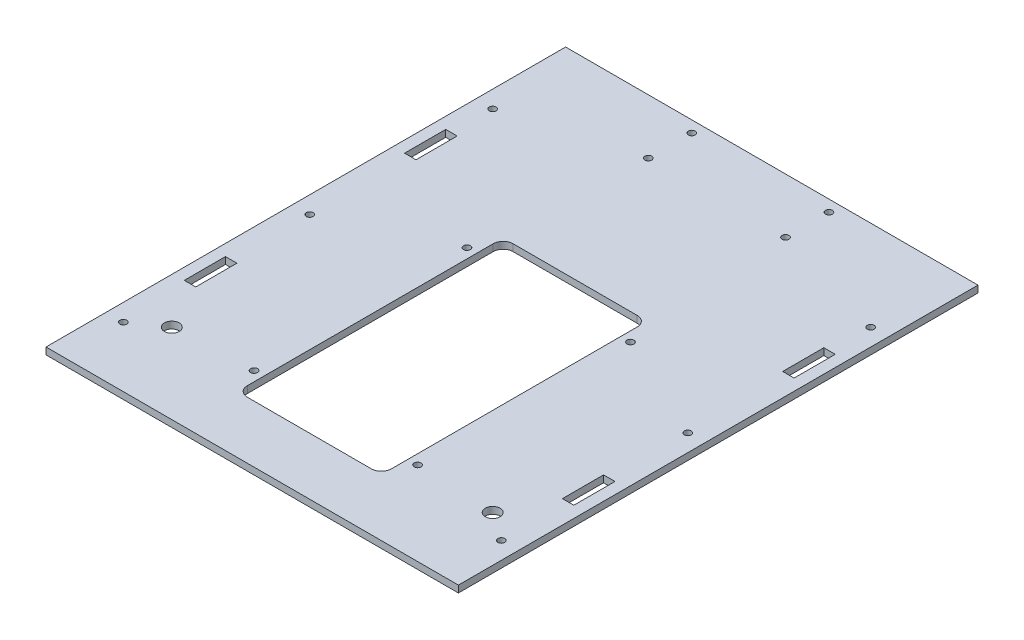
SolidWorks part; units mm, degrees
material "PMMA"
ref_plane "Front Plane" through (0, 0, 0) normal (0, 0, 1) x (1, 0, 0)
ref_plane "Top Plane" through (0, 0, 0) normal (0, 1, 0) x (1, 0, 0)
ref_plane "Right Plane" through (0, 0, 0) normal (1, 0, 0) x (0, 0, -1)
sketch "Schizzo1" plane through (0, 0, 0) normal (0, 1, 0) x (1, 0, 0)
  line L0 (90.17, 113.61) -> (-90.17, -113.61) construction
  line L1 (-90.17, 113.61) -> (90.17, 113.61)
  line L2 (-90.17, 113.61) -> (-90.17, -113.61)
  line L3 (-90.17, -113.61) -> (90.17, -113.61)
  line L4 (90.17, 113.61) -> (90.17, -113.61)
  point P4 (0, 0)
  dimension "D1" = 227.22
  dimension "D2" = 180.34
extrude "Estrusione-Estrusione1" add sketch "Schizzo1" along normal blind 3
sketch "Schizzo3" plane through (0, 0, 0) normal (0, 1, 0) x (1, 0, 0)
  line L0 (0, 113.61) -> (0, -113.61) construction
  line L1 (-31.5, -88.61) -> (-31.5, 27.62) construction
  line L2 (-31.5, -88.61) -> (31.5, -88.61) construction
  line L3 (31.5, -88.61) -> (31.5, 27.62) construction
  line L4 (-31.5, 27.62) -> (31.5, 27.62) construction
  line L5 (90.17, 113.61) -> (-90.17, 113.61) construction
  line L6 (-90.17, -113.61) -> (90.17, -113.61) construction
  line L7 (-31.5, -84.26) -> (-31.5, 23.27)
  line L8 (-27.15, -88.61) -> (27.15, -88.61)
  line L9 (31.5, -84.26) -> (31.5, 23.27)
  line L10 (-27.15, 27.62) -> (27.15, 27.62)
  line L11 (-35.75, -77.045) -> (35.75, -77.045) construction
  line L12 (0, 27.62) -> (0, -88.61) construction
  line L13 (-35.75, 16.055) -> (-35.75, -77.045) construction
  line L14 (-35.75, 16.055) -> (35.75, 16.055) construction
  line L15 (35.75, -77.045) -> (35.75, 16.055) construction
  arc A0 (-31.5, -84.26) -> (-27.15, -88.61) centre (-27.15, -84.26) ccw
  arc A1 (31.5, -84.26) -> (27.15, -88.61) centre (27.15, -84.26) cw
  arc A2 (27.15, 27.62) -> (31.5, 23.27) centre (27.15, 23.27) cw
  arc A3 (-31.5, 23.27) -> (-27.15, 27.62) centre (-27.15, 23.27) cw
  circle A4 centre (-35.75, -77.045) radius 1.5
  circle A5 centre (35.75, -77.045) radius 1.5
  circle A6 centre (-35.75, 16.055) radius 1.5
  circle A7 centre (35.75, 16.055) radius 1.5
  point P29 (0, -77.045)
  dimension "D12" = 3
  dimension "D1" = 116.23
  dimension "D2" = 63
  dimension "D4" = 4.35
  dimension "D5" = 4.35
  dimension "D6" = 4.35
  dimension "D7" = 4.35
  dimension "D8" = 4.35
  dimension "D9" = 4.35
  dimension "D10" = 4.35
  dimension "D11" = 4.35
  dimension "D13" = 71.5
  dimension "D14" = 93.1
  dimension "D3" = 25
  dimension "D15" = 116.23
  dimension "D16" = 11.565
  dimension "D17" = 11.565
sketch "Schizzo2" plane through (0, 0, 0) normal (0, 1, 0) x (1, 0, 0)
  line L0 (90.17, -113.61) -> (90.17, 113.61) construction
  line L1 (85.17, -40.13) -> (80.17, -40.13)
  line L2 (85.17, -40.13) -> (85.17, -58.13)
  line L3 (85.17, -58.13) -> (80.17, -58.13)
  line L4 (80.17, -40.13) -> (80.17, -58.13)
  line L5 (-90.17, -113.61) -> (90.17, -113.61) construction
  line L6 (0, -113.61) -> (0, 113.61) construction
  line L7 (90.17, 113.61) -> (-90.17, 113.61) construction
  line L8 (-85.17, -40.13) -> (-80.17, -40.13)
  line L9 (-85.17, -40.13) -> (-85.17, -58.13)
  line L10 (-85.17, -58.13) -> (-80.17, -58.13)
  line L11 (-80.17, -40.13) -> (-80.17, -58.13)
  line L12 (-82.67, 113.61) -> (-82.67, -113.61) construction
  line L13 (-90.17, -78.61) -> (90.17, -78.61) construction
  line L14 (-85.17, 38.19) -> (-80.17, 38.19)
  line L15 (-85.17, 38.19) -> (-85.17, 56.19)
  line L16 (-85.17, 56.19) -> (-80.17, 56.19)
  line L17 (-80.17, 38.19) -> (-80.17, 56.19)
  line L18 (85.17, 38.19) -> (80.17, 38.19)
  line L19 (80.17, 38.19) -> (80.17, 56.19)
  line L20 (85.17, 56.19) -> (80.17, 56.19)
  line L21 (85.17, 38.19) -> (85.17, 56.19)
  line L22 (0, 103.9337) -> (0, 44.5482) construction
  line L23 (-90.17, 113.61) -> (-90.17, -113.61) construction
  circle A0 centre (-82.67, -5.81) radius 1.5
  circle A1 centre (-82.67, -87.31) radius 1.5
  circle A2 centre (-82.67, 74.19) radius 1.5
  circle A3 centre (82.67, -87.31) radius 1.5
  circle A4 centre (82.67, -5.81) radius 1.5
  circle A5 centre (82.67, 74.19) radius 1.5
  circle A6 centre (-70.17, -78.61) radius 3.25
  circle A7 centre (70.17, -78.61) radius 3.25
  circle A8 centre (-30, 89.61) radius 1.5
  circle A9 centre (-30, 108.61) radius 1.5
  circle A10 centre (30, 89.61) radius 1.5
  circle A11 centre (30, 108.61) radius 1.5
  point P18 (-82.67, -58.13)
  dimension "D6" = 3
  dimension "D11" = 6.5
  dimension "D13" = 3
  dimension "D1" = 5
  dimension "D2" = 5
  dimension "D4" = 18
  dimension "D3" = 55.48
  dimension "D5" = 57.42
  dimension "D7" = 26.3
  dimension "D8" = 107.8
  dimension "D9" = 187.8
  dimension "D10" = 35
  dimension "D12" = 20
  dimension "D14" = 30
  dimension "D15" = 19
  dimension "D16" = 5
extrude "Taglio-Estrusione1" cut sketch "Schizzo2" along direction (0, 1, 0) on the side of the normal through all
extrude "Taglio-Estrusione5" cut sketch "Schizzo3" along direction (0, 1, 0) on the side of the normal through all
equation "\"Thickness5\"=5"
equation "\"D1@Estrusione-Estrusione1\"=\"Thickness3\""
equation "\"D1@Schizzo2\"=\"Thickness5\""
equation "\"D2@Schizzo2\"=\"Thickness5\""
equation "\"Thickness3\"=3"
equation "\"D5@Schizzo3\"=\"D4@Schizzo3\""
equation "\"D6@Schizzo3\"=\"D5@Schizzo3\""
equation "\"D7@Schizzo3\"=\"D6@Schizzo3\""
equation "\"D8@Schizzo3\"=\"D7@Schizzo3\""
equation "\"D9@Schizzo3\"=\"D8@Schizzo3\""
equation "\"D10@Schizzo3\"=\"D9@Schizzo3\""
equation "\"D11@Schizzo3\"=\"D10@Schizzo3\""
